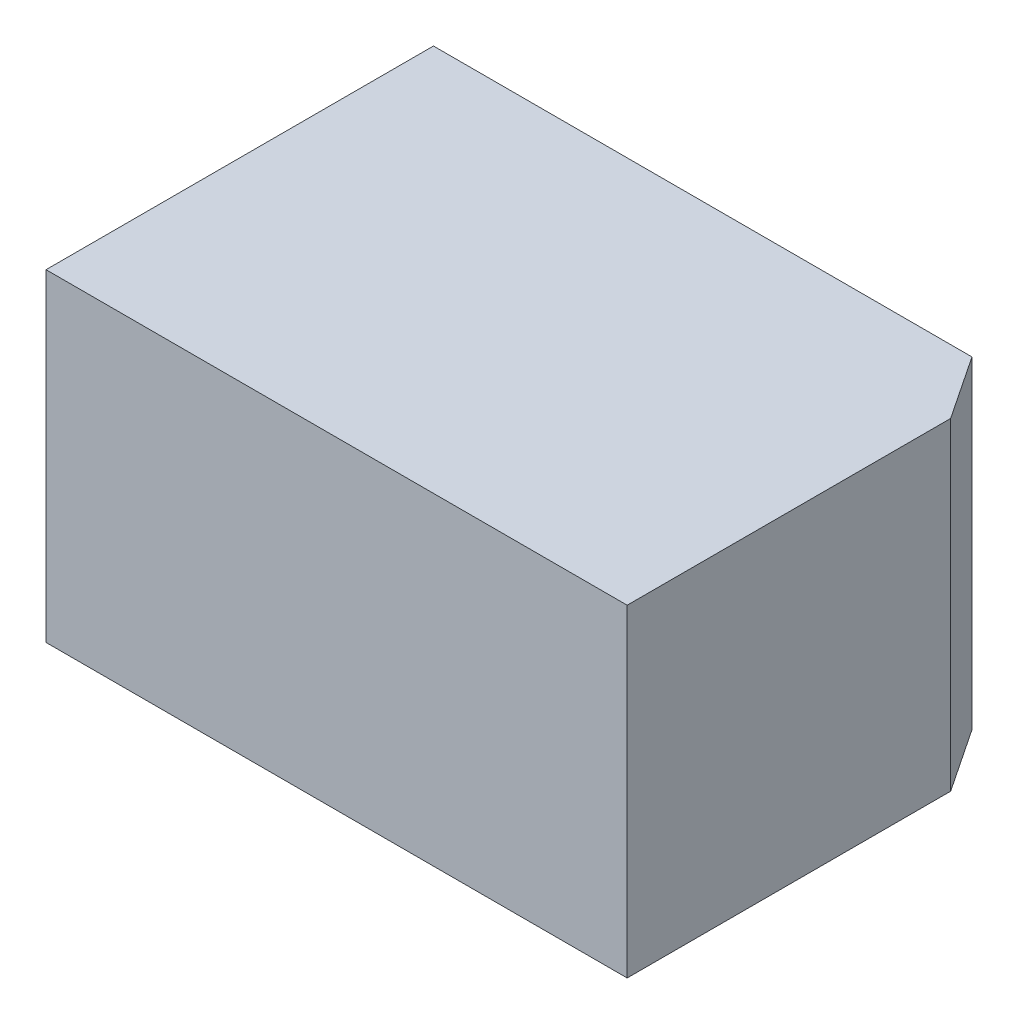
SolidWorks part; units mm, degrees
ref_plane "Front Plane" through (0, 0, 0) normal (0, 0, 1) x (1, 0, 0)
ref_plane "Top Plane" through (0, 0, 0) normal (0, 1, 0) x (1, 0, 0)
ref_plane "Right Plane" through (0, 0, 0) normal (1, 0, 0) x (0, 0, -1)
sketch "Sketch1" plane through (0, 0, 0) normal (0, 1, 0) x (1, 0, 0)
  line L1 (4.5, 3) -> (-4.5, 3)
  line L2 (4.5, 3) -> (4.5, -3)
  line L3 (4.5, -3) -> (-4.5, -3)
  line L4 (-4.5, 3) -> (-4.5, -3)
  line L5 (4.5, 3) -> (-4.5, -3) construction
  line L6 (4.5, -3) -> (-4.5, 3) construction
  point P0 (0, 0)
  dimension "D1" = 6
  dimension "D2" = 9
extrude "Boss-Extrude1" add sketch "Sketch1" along normal blind 5
sketch "Sketch3" plane through (0, 0, 0) normal (0, -1, 0) x (1, 0, 0)
  line L0 (-4.5, -3) -> (-4.5, 3) construction
  line L1 (0, 0) -> (-1.5, 0) construction
  circle A0 centre (-1.5, 0) radius 1.25
  dimension "D1" = 2.5
  dimension "D2" = 3
extrude "Cut-Extrude2" cut sketch "Sketch3" against normal blind 4
sketch "Sketch2" plane through (0, 0, 0) normal (0, -1, 0) x (1, 0, 0)
  line L0 (-3.25, 1.875) -> (-3.25, -1.875) construction
  line L1 (1.5, 0) -> (-1.5, 0) construction
  line L2 (-1.5, 0) -> (-3.25, 0) construction
  circle A0 centre (-3.25, -1.875) radius 0.795
  circle A1 centre (-3.25, 1.875) radius 0.795
  circle A2 centre (1.5, 0) radius 0.795
  circle A3 centre (-1.5, 0) radius 1.25 construction
  dimension "D4" = 1.59
  dimension "D1" = 3.75
  dimension "D2" = 3
  dimension "D3" = 1.75
extrude "Cut-Extrude1" cut sketch "Sketch2" against normal blind 1
sketch "Sketch4" plane through (0, 0, 0) normal (0, -1, 0) x (1, 0, 0)
  line L0 (-4.5, 3) -> (4.5, -3) construction
  line L1 (4.5, 3) -> (4.5, -3) construction
  line L4 (4.5, -3) -> (-4.5, -3) construction
  line L5 (3.8399, -3) -> (4.5, -2.0099)
  line L6 (4.5, -2.0099) -> (4.5, -3)
  line L7 (4.5, -3) -> (3.8399, -3)
  dimension "D1" = 1.19
extrude "Cut-Extrude3" cut sketch "Sketch4" against normal through all
